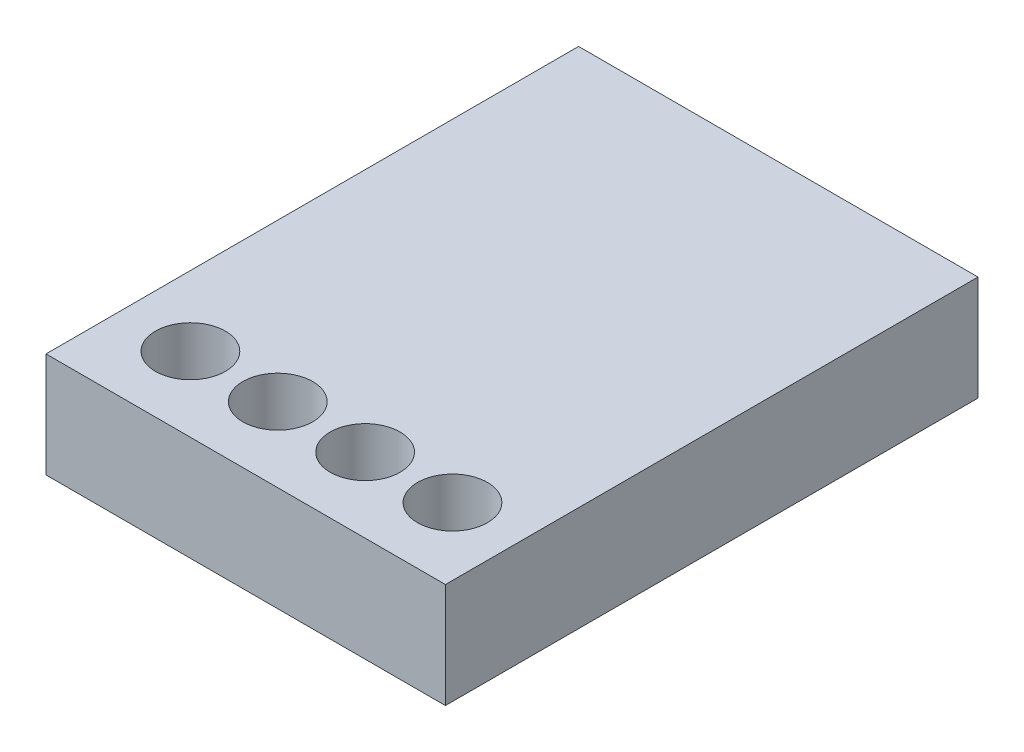
SolidWorks part; units mm, degrees
ref_plane "Front Plane" through (0, 0, 0) normal (0, 0, 1) x (1, 0, 0)
ref_plane "Top Plane" through (0, 0, 0) normal (0, 1, 0) x (1, 0, 0)
ref_plane "Right Plane" through (0, 0, 0) normal (1, 0, 0) x (0, 0, -1)
sketch "Sketch1" plane through (0, 0, 0) normal (0, 1, 0) x (1, 0, 0)
  line L1 (-5.8942, 4.3609) -> (5.5358, 4.3609)
  line L2 (-5.8942, 4.3609) -> (-5.8942, -10.8791)
  line L3 (-5.8942, -10.8791) -> (5.5358, -10.8791)
  line L4 (5.5358, 4.3609) -> (5.5358, -10.8791)
  dimension "D1" = 11.43
  dimension "D2" = 15.24
extrude "Boss-Extrude1" add sketch "Sketch1" along normal blind 3
sketch "Sketch2" plane through (0, 3, 0) normal (0, 1, 0) x (1, 0, 0)
  line L0 (5.5358, -10.8791) -> (5.5358, 4.3609) construction
  circle A0 centre (-3.8942, -8.7471) radius 1
  circle A1 centre (-1.3942, -8.7471) radius 1
  circle A2 centre (1.1058, -8.7471) radius 1
  circle A3 centre (3.6058, -8.7471) radius 1
  dimension "D1" = 2
  dimension "D2" = 2
  dimension "D3" = 2
  dimension "D4" = 2
  dimension "D5" = 2
  dimension "D6" = 2.5
  dimension "D7" = 2.5
  dimension "D8" = 2.5
  dimension "D9" = 1.93
extrude "Cut-Extrude1" cut sketch "Sketch2" against normal blind 10
